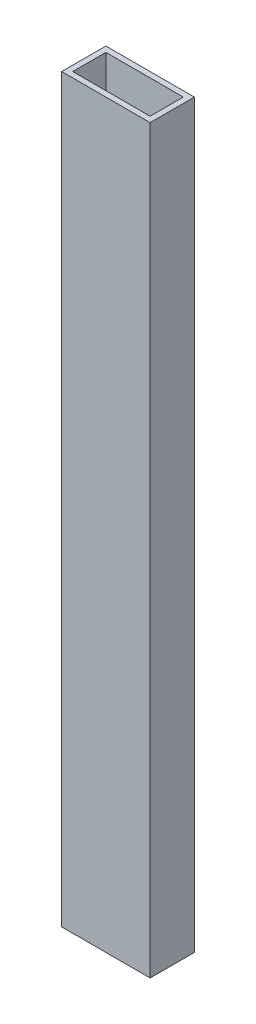
SolidWorks part; units mm, degrees
ref_plane "Front Plane" through (0, 0, 0) normal (0, 0, 1) x (1, 0, 0)
ref_plane "Top Plane" through (0, 0, 0) normal (0, 1, 0) x (1, 0, 0)
ref_plane "Right Plane" through (0, 0, 0) normal (1, 0, 0) x (0, 0, -1)
sketch "Sketch1" plane through (0, 0, 0) normal (0, 1, 0) x (1, 0, 0)
  line L1 (0, 0) -> (50.8, 0)
  line L2 (0, 0) -> (0, 25.4)
  line L3 (0, 25.4) -> (50.8, 25.4)
  line L4 (50.8, 0) -> (50.8, 25.4)
  line L5 (3.175, 22.225) -> (47.625, 22.225)
  line L6 (3.175, 22.225) -> (3.175, 3.175)
  line L7 (3.175, 3.175) -> (47.625, 3.175)
  line L8 (47.625, 22.225) -> (47.625, 3.175)
  dimension "D1" = 3.175
  dimension "D2" = 3.175
  dimension "D3" = 3.175
  dimension "D4" = 3.175
  dimension "D5" = 50.8
  dimension "D6" = 25.4
extrude "Boss-Extrude1" add sketch "Sketch1" along normal blind 425.45
